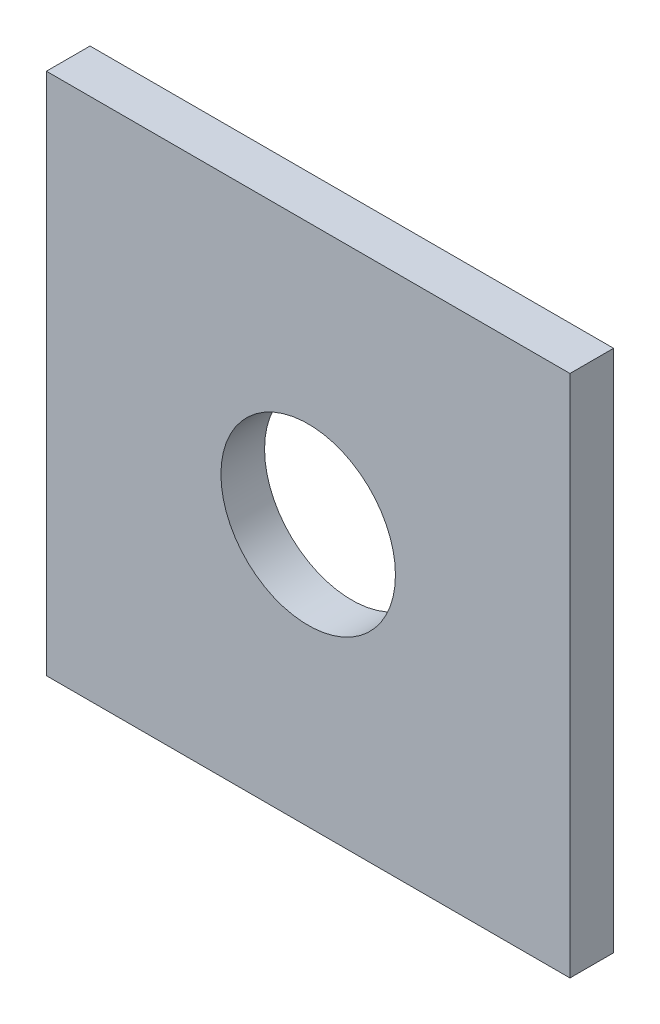
SolidWorks part; units mm, degrees
ref_plane "Front Plane" through (0, 0, 0) normal (0, 0, 1) x (1, 0, 0)
ref_plane "Top Plane" through (0, 0, 0) normal (0, 1, 0) x (1, 0, 0)
ref_plane "Right Plane" through (0, 0, 0) normal (1, 0, 0) x (0, 0, -1)
sketch "Sketch1" plane through (0, 0, 0) normal (0, 0, 1) x (1, 0, 0)
  line L0 (152.4, 76.2) -> (58.4333, 76.2) construction
  line L1 (0, 0) -> (152.4, 0)
  line L2 (0, 0) -> (0, 152.4)
  line L3 (0, 152.4) -> (152.4, 152.4)
  line L4 (152.4, 0) -> (152.4, 152.4)
  line L5 (76.2, 0) -> (76.2, 76.2) construction
  dimension "D1" = 152.4
  dimension "D2" = 152.4
extrude "Boss-Extrude1" add sketch "Sketch1" along normal blind 12.7
sketch "Sketch2" plane through (0, 0, 0) normal (0, 0, -1) x (-1, 0, 0)
  line L0 (-152.4, 76.2) -> (-37.9725, 76.2) construction
  line L1 (-152.4, 0) -> (-152.4, 152.4) construction
  line L2 (-76.2, 0) -> (-76.2, 76.2) construction
  line L4 (0, 0) -> (-152.4, 0) construction
  circle A0 centre (-76.2, 76.2) radius 25.4
extrude "Cut-Extrude1" cut sketch "Sketch2" against normal blind 12.7
